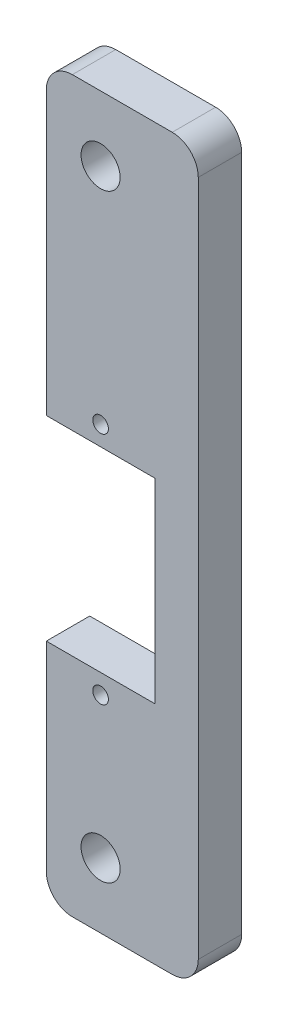
SolidWorks part; units mm, degrees
ref_plane "Front Plane" through (0, 0, 0) normal (0, 0, 1) x (1, 0, 0)
ref_plane "Top Plane" through (0, 0, 0) normal (0, 1, 0) x (1, 0, 0)
ref_plane "Right Plane" through (0, 0, 0) normal (1, 0, 0) x (0, 0, -1)
sketch "Sketch2" plane through (0, 0, 0) normal (0, 0, 1) x (1, 0, 0)
  line L0 (-11.25, 46.75) -> (-11.25, 6.25) construction
  line L1 (-11.25, 46.75) -> (11.25, 46.75)
  line L2 (-11.25, 6.25) -> (-6.25, 6.25) construction
  line L3 (-11.25, -37.25) -> (11.25, -37.25)
  line L4 (11.25, 46.75) -> (11.25, -37.25)
  line L5 (-6.25, 11.25) -> (6.25, 11.25)
  line L6 (-6.25, 6.25) -> (-6.25, 11.25) construction
  line L7 (-6.25, -11.25) -> (6.25, -11.25)
  line L8 (6.25, 11.25) -> (6.25, -11.25)
  line L9 (-6.25, -11.25) -> (-6.25, -6.25) construction
  line L10 (-6.25, -6.25) -> (-11.25, -6.25) construction
  line L11 (-11.25, -6.25) -> (-11.25, -37.25) construction
  line L12 (0, -29.75) -> (0, -37.25) construction
  line L13 (0, 39.25) -> (0, 46.75) construction
  line L14 (6.25, 0) -> (11.25, 0) construction
  line L15 (0, 13.5) -> (0, -13.5) construction
  line L16 (-6.25, -37.25) -> (-6.25, -11.25)
  line L17 (-6.25, 11.25) -> (-6.25, 46.75)
  point P12 (6.25, 0)
  point P13 (0, 11.25)
  point P15 (0, -29.75)
  point P16 (0, 39.25)
  point P17 (0, -5.25)
  point P18 (0, -11.25)
  point P25 (0, 13.5)
  point P26 (0, -13.5)
  dimension "D1" = 12.5
  dimension "D2" = 22.5
  dimension "D3" = 69
  dimension "D4" = 6
  dimension "D5" = 24.5
  dimension "D6" = 7.5
  dimension "D7" = 5
  dimension "D8" = 5
  dimension "D9" = 27
extrude "Boss-Extrude1" add sketch "Sketch2" along normal blind 5 contours L17 L5 L8 L7 L16 L3 L4 L1
hole_wizard "M4 Clearance Hole1" positions "Sketch4" profile "Sketch3" hole size "M4" standard "ANSI Metric" end condition through all
sketch "Sketch4" plane through (0, 0, 0) normal (0, 0, 1) x (1, 0, 0)
  point P1 (0, 39.25)
  point P3 (0, -29.75)
sketch "Sketch3" plane through (0, 39.25, 0) normal (1, 0, 0) x (0, 1, 0)
  line L0 (0, 0) -> (0, 5)
  line L1 (0, 5) -> (2.25, 5)
  line L2 (2.25, 5) -> (2.25, 0)
  line L5 (2.25, 0) -> (0, 0)
  line L11 (0, -6.35) -> (0, 107.95) construction
  dimension "Thru Hole Dia." = 4.5
  dimension "Thru Hole Depth" = 5
fillet "Fillet1" radius 3 4 edges at (11.25, 46.75, 2.5) (11.25, -37.25, 2.5) (-6.25, -37.25, 2.5) (-6.25, 46.75, 2.5)
hole_wizard "M1.6 Clearance Hole1" positions "Sketch6" profile "Sketch5" hole size "M1.6" standard "ANSI Metric" end condition through all
sketch "Sketch6" plane through (0, 0, 0) normal (0, 0, 1) x (1, 0, 0)
  point P1 (0, 13.5)
  point P3 (0, -13.5)
sketch "Sketch5" plane through (0, 13.5, 0) normal (1, 0, 0) x (0, 1, 0)
  line L0 (0, 0) -> (0, 5)
  line L1 (0, 5) -> (0.9, 5)
  line L2 (0.9, 5) -> (0.9, 0)
  line L5 (0.9, 0) -> (0, 0)
  line L11 (0, -6.35) -> (0, 107.95) construction
  dimension "Thru Hole Dia." = 1.8
  dimension "Thru Hole Depth" = 5
equation "\"d_slots\" = 69mm"
equation "\"w_servo\"= 12.5mm"
equation "\"l_servo\"= 22.5mm"
equation "\"D1@Sketch2\"=\"w_servo\""
equation "\"D2@Sketch2\"=\"l_servo\""
equation "\"D3@Sketch2\"=\"d_slots\""
equation "\"D4@Sketch2\"=\"d_servocenter\""
equation "\"d_servocenter\"= 6mm"
equation "\"d_centertoslot\"= 24.5mm"
equation "\"D5@Sketch2\"=\"d_centertoslot\""
